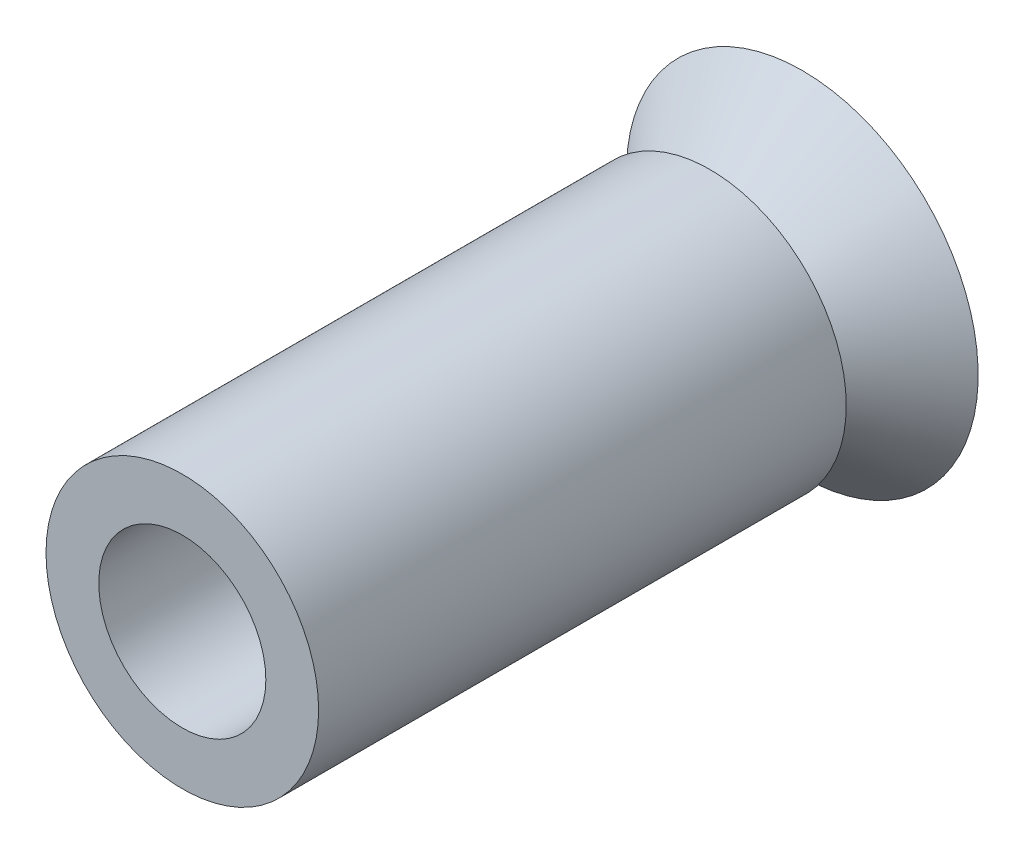
SolidWorks part; units mm, degrees
ref_plane "Front Plane" through (0, 0, 0) normal (0, 0, 1) x (1, 0, 0)
ref_plane "Top Plane" through (0, 0, 0) normal (0, 1, 0) x (1, 0, 0)
ref_plane "Right Plane" through (0, 0, 0) normal (1, 0, 0) x (0, 0, -1)
sketch "Sketch3" plane through (0, 0, 0) normal (1, 0, 0) x (0, 0, -1)
  line L0 (0, 2) -> (-1.05, 0.95)
  line L1 (0, 0) -> (-1.05, 0)
  line L2 (-1.05, 0.95) -> (-1.05, 0)
  line L4 (0, 0) -> (0, 2)
  point P2 (-0.35, 1.65)
  point P8 (-1.05, 0.95)
  dimension "D1" = 0.95
  dimension "D2" = 45
  dimension "D3" = 2
  dimension "D4" = 1.65
revolve "Revolve1" add sketch "Sketch3" angle 360 about L1
sketch "Sketch5" plane through (0, 0, 1.05) normal (0, 0, 1) x (1, 0, 0)
  circle A0 centre (0, 0) radius 0.95
extrude "Boss-Extrude1" add sketch "Sketch5" along normal blind 3 from surface at -1.05 starting at face at (0, 2, 0)
ref_plane "Plane1" through (0, 0, 0.35) normal (0, 0, 1) x (1, 0, 0)
sketch "Sketch7" plane through (0, 0, 0.35) normal (0, 0, 1) x (1, 0, 0)
  circle A0 centre (0, 0) radius 1.55
  circle A1 centre (0, 0) radius 0.95
  dimension "D1" = 3.1
  dimension "D2" = 1.9
extrude "Boss-Extrude2" add sketch "Sketch7" along normal blind 6 from vertex at 0.7 separate body starting at point (0, 0.95, 1.05)
equation "\"D4@Sketch3\"=3.3/2"
